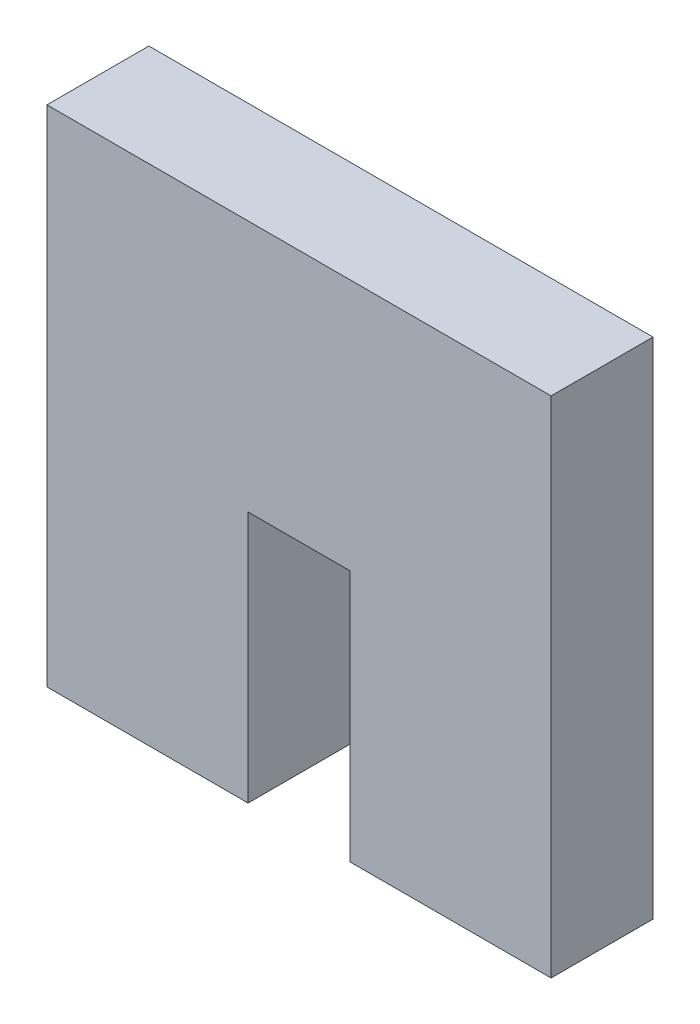
SolidWorks part; units mm, degrees
material "Balsa"
ref_plane "Front Plane" through (0, 0, 0) normal (0, 0, 1) x (1, 0, 0)
ref_plane "Top Plane" through (0, 0, 0) normal (0, 1, 0) x (1, 0, 0)
ref_plane "Right Plane" through (0, 0, 0) normal (1, 0, 0) x (0, 0, -1)
sketch "Sketch1" plane through (0, 0, 0) normal (0, 0, 1) x (1, 0, 0)
  line L0 (8.521, 5.34) -> (0, 5.34) construction
  line L1 (0, 0) -> (8.521, 0)
  line L2 (0, 0) -> (0, 21.36)
  line L3 (0, 21.36) -> (21.36, 21.36)
  line L4 (21.36, 0) -> (21.36, 21.36)
  line L6 (8.521, 0) -> (8.521, 10.68)
  line L7 (8.521, 10.68) -> (12.839, 10.68)
  line L8 (12.839, 0) -> (12.839, 10.68)
  line L9 (12.839, 5.34) -> (21.36, 5.34) construction
  line L10 (12.839, 0) -> (21.36, 0)
  dimension "D1" = 21.36
  dimension "D2" = 21.36
  dimension "D3" = 10.68
  dimension "D4" = 4.318
extrude "Boss-Extrude1" add sketch "Sketch1" along normal blind 4.318
